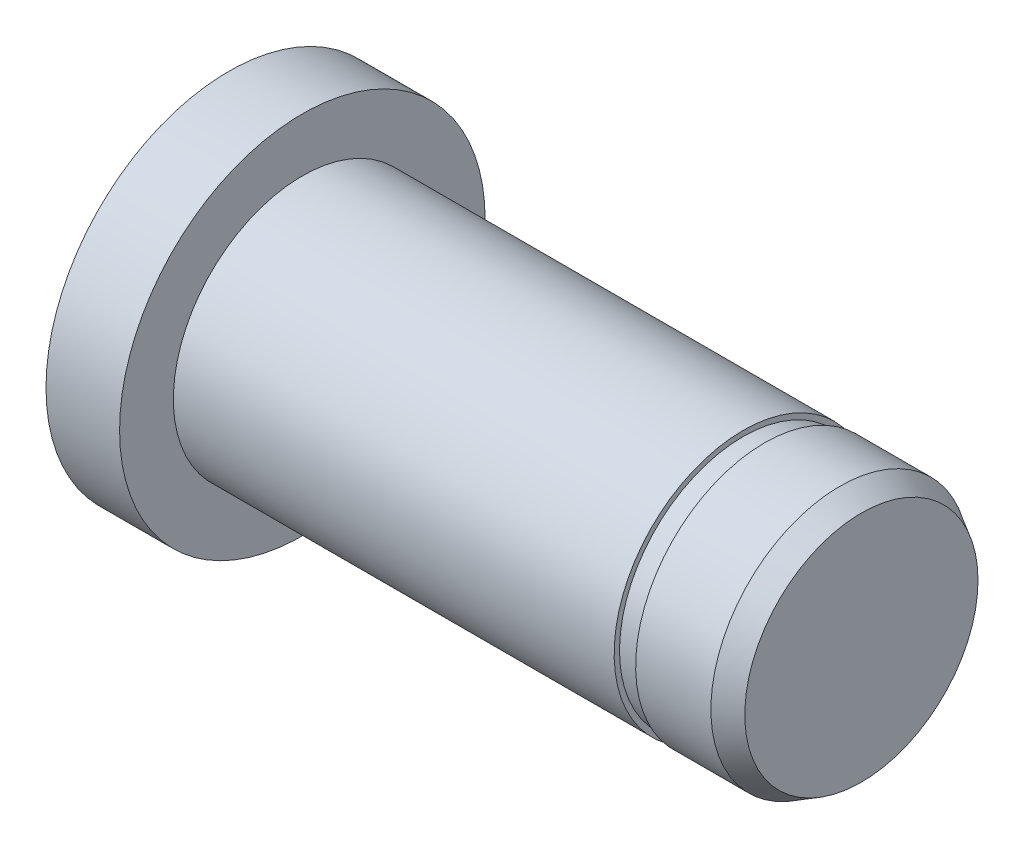
SolidWorks part; units mm, degrees
ref_plane "Płaszczyzna przednia" through (0, 0, 0) normal (0, 0, 1) x (1, 0, 0)
ref_plane "Płaszczyzna górna" through (0, 0, 0) normal (0, 1, 0) x (1, 0, 0)
ref_plane "Płaszczyzna prawa" through (0, 0, 0) normal (1, 0, 0) x (0, 0, -1)
sketch "Szkic1" plane through (0, 0, 0) normal (0, 0, 1) x (1, 0, 0)
  line L0 (0, 0) -> (0, 8.5)
  line L1 (0, 8.5) -> (4, 8.5)
  line L2 (4, 8.5) -> (4, 6)
  line L3 (4, 6) -> (30, 6)
  line L4 (30, 6) -> (30, 0)
  line L5 (30, 0) -> (0, 0)
  dimension "D1" = 4
  dimension "D2" = 8.5
  dimension "D3" = 6
  dimension "D4" = 26
revolve "Obrót1" add sketch "Szkic1" angle 360 about L5
chamfer "Sfazowanie1" distance 1 angle 30 2 edges at (30, 0, -6) (0, 0, -8.5)
sketch "Szkic2" plane through (30, 0, 0) normal (1, 0, 0) x (0, 0, -1)
  circle A0 centre (0, 0) radius 6
  circle A1 centre (0, 0) radius 5.75
  dimension "D1" = 12
  dimension "D2" = 11.5
extrude "Wytnij-wyciągnięcie1" cut sketch "Szkic2" against normal blind 1 from offset 4.5 offset against normal yes
